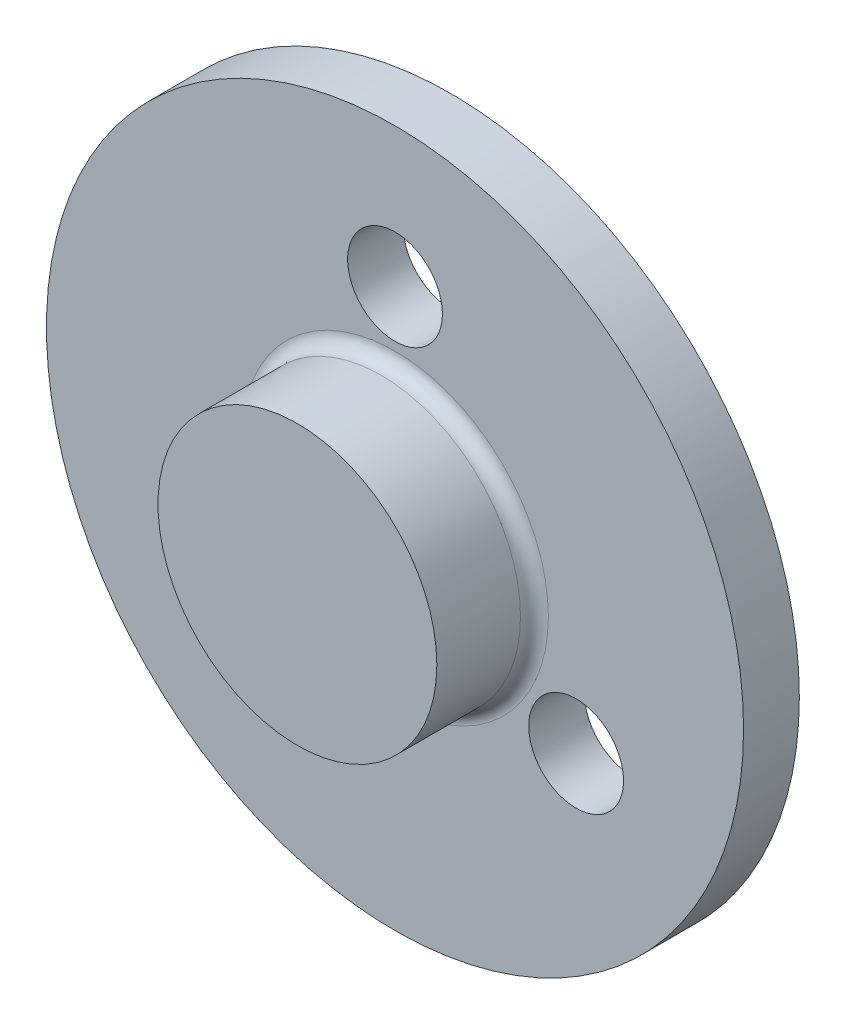
SolidWorks part; units mm, degrees
ref_plane "Front Plane" through (0, 0, 0) normal (0, 0, 1) x (1, 0, 0)
ref_plane "Top Plane" through (0, 0, 0) normal (0, 1, 0) x (1, 0, 0)
ref_plane "Right Plane" through (0, 0, 0) normal (1, 0, 0) x (0, 0, -1)
sketch "Sketch1" plane through (0, 0, 0) normal (0, 0, 1) x (1, 0, 0)
  circle A0 centre (0, 0) radius 25
  circle A1 centre (0, 0) radius 15 construction
  dimension "D1" = 50
  dimension "D2" = 30
extrude "Boss-Extrude1" add sketch "Sketch1" against normal blind 4
sketch "Sketch2" plane through (0, 0, 0) normal (0, 0, 1) x (1, 0, 0)
  circle A0 centre (0, 0) radius 10
  dimension "D1" = 20
extrude "Boss-Extrude2" add sketch "Sketch2" along normal blind 7
fillet "Fillet1" radius 1 1 edges at (10, 0, 0)
sketch "Sketch3" plane through (0, 0, -4) normal (0, 0, -1) x (-1, 0, 0)
  circle A0 centre (0, 0) radius 7.5
  dimension "D1" = 15
extrude "Cut-Extrude1" cut sketch "Sketch3" against normal blind 5
sketch "Sketch5" plane through (0, 0, 0) normal (0, 0, 1) x (1, 0, 0)
  circle A0 centre (0, 0) radius 15
  point P3 (0, 15)
  point P6 (12.9904, -7.5)
  point P7 (-12.9904, -7.5)
  dimension "D1" = 30
  dimension "D2" = 3
hole_wizard "Ø6.0mm Dowel Hole1" positions "Sketch5" profile "Sketch6" hole size "Ø6.0" standard "ISO" end condition through all
sketch "Sketch6" plane through (-12.9904, -7.5, 0) normal (1, 0, 0) x (0, -1, 0)
  line L0 (0, 0) -> (0, 4)
  line L1 (0, 4) -> (3.4, 4)
  line L2 (3.4, 4) -> (3.4, 0)
  line L5 (3.4, 0) -> (0, 0)
  line L11 (0, -6.35) -> (0, 107.95) construction
  dimension "Thru Hole Dia." = 6.8
  dimension "Thru Hole Depth" = 4
